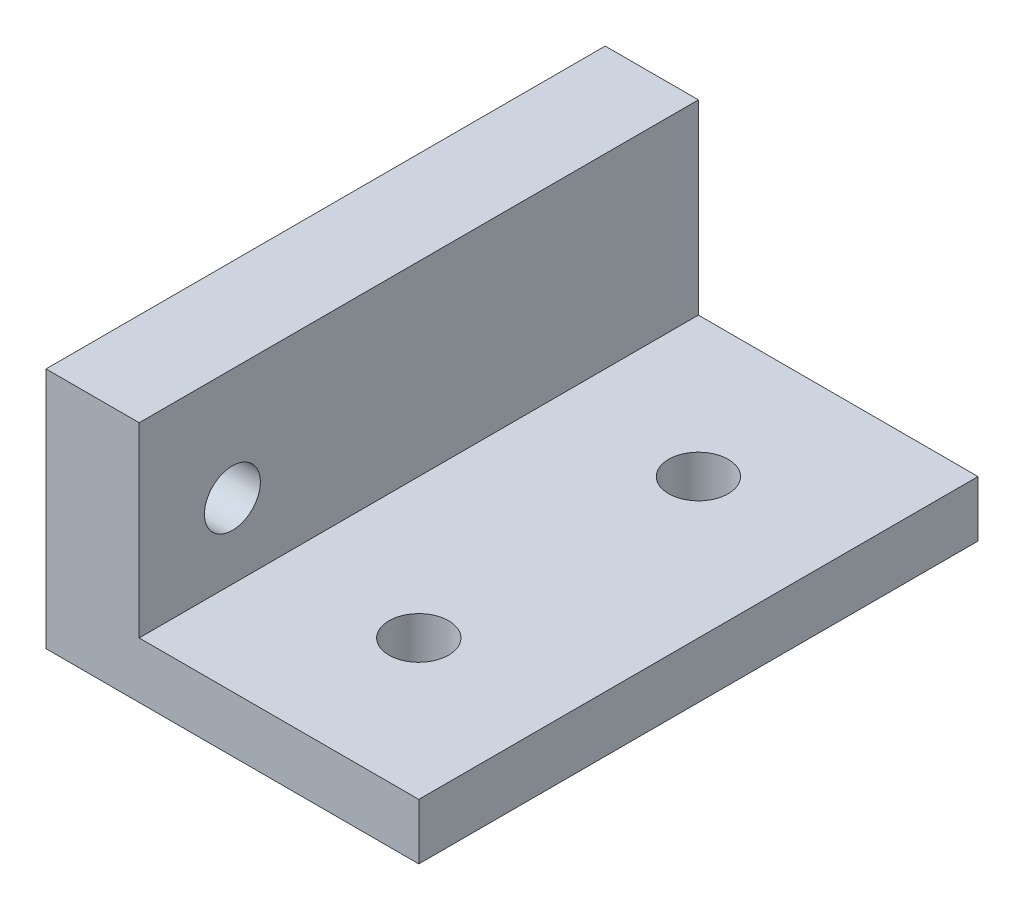
SolidWorks part; units mm, degrees
ref_plane "Front Plane" through (0, 0, 0) normal (0, 0, 1) x (1, 0, 0)
ref_plane "Top Plane" through (0, 0, 0) normal (0, 1, 0) x (1, 0, 0)
ref_plane "Right Plane" through (0, 0, 0) normal (1, 0, 0) x (0, 0, -1)
sketch "Sketch1" plane through (0, 0, 0) normal (0, 1, 0) x (1, 0, 0)
  line L1 (-10, 15) -> (10, 15)
  line L2 (-10, 15) -> (-10, -15)
  line L3 (-10, -15) -> (10, -15)
  line L4 (10, 15) -> (10, -15)
  line L5 (-10, 15) -> (10, -15) construction
  line L6 (-10, -15) -> (10, 15) construction
  point P0 (0, 0)
  dimension "D1" = 20
  dimension "D2" = 30
extrude "Boss-Extrude1" add sketch "Sketch1" along normal blind 3
sketch "Sketch2" plane through (0, 3, 0) normal (0, 1, 0) x (1, 0, 0)
  line L0 (-10, -15) -> (10, -15) construction
  line L1 (-10, 15) -> (-5, 15)
  line L2 (-10, 15) -> (-10, -15)
  line L3 (-10, -15) -> (-5, -15)
  line L4 (-5, 15) -> (-5, -15)
  dimension "D1" = 5
extrude "Boss-Extrude2" add sketch "Sketch2" along normal blind 10
sketch "Sketch3" plane through (-10, 0, 0) normal (-1, 0, 0) x (0, 0, 1)
  line L0 (-15, 7) -> (15, 7) construction
  line L1 (-15, 13) -> (-15, 0) construction
  line L2 (15, 13) -> (15, 0) construction
  line L4 (-15, 0) -> (15, 0) construction
  circle A0 centre (10, 7) radius 1.5
  dimension "D2" = 5
  dimension "D3" = 3
  dimension "D1" = 7
extrude "Cut-Extrude1" cut sketch "Sketch3" against normal blind 10
sketch "Sketch4" plane through (0, 3, 0) normal (0, 1, 0) x (1, 0, 0)
  line L1 (-5, -15) -> (10, -15) construction
  line L2 (10, 15) -> (-5, 15) construction
  line L3 (10, -15) -> (10, 15) construction
  circle A0 centre (2.5, -7.5) radius 1.6
  circle A1 centre (2.5, 7.5) radius 1.6
  dimension "D1" = 3.2
  dimension "D2" = 3.2
  dimension "D3" = 7.5
  dimension "D4" = 7.5
  dimension "D5" = 7.5
  dimension "D6" = 7.5
extrude "Cut-Extrude2" cut sketch "Sketch4" against normal through all
